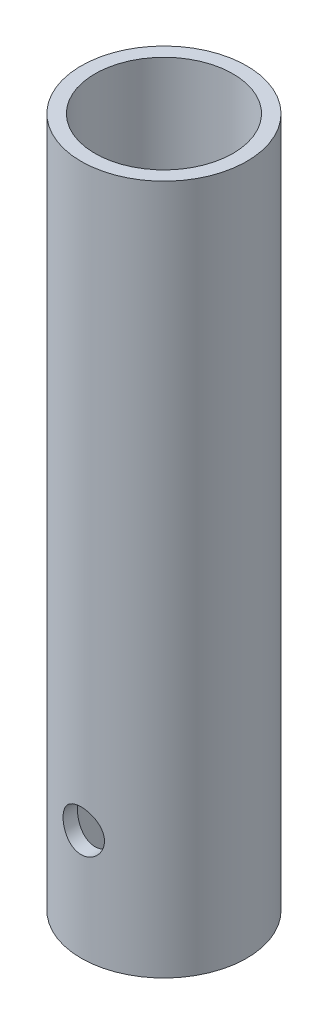
SolidWorks part; units mm, degrees
ref_plane "Ön Düzlem" through (0, 0, 0) normal (0, 0, 1) x (1, 0, 0)
ref_plane "Üst Düzlem" through (0, 0, 0) normal (0, 1, 0) x (1, 0, 0)
ref_plane "Sağ Düzlem" through (0, 0, 0) normal (1, 0, 0) x (0, 0, -1)
sketch "Sketch1" plane through (0, 0, 0) normal (0, 1, 0) x (1, 0, 0)
  circle A0 centre (0, 0) radius 6
  dimension "D1" = 12
extrude "Extrude-Thin1" add sketch "Sketch1" along normal blind 50 thin thin type one direction reverse wall 1
sketch "Sketch2" plane through (0, 0, 0) normal (0, 0, 1) x (1, 0, 0)
  circle A0 centre (0, 8) radius 1.5
  dimension "D1" = 3
  dimension "D2" = 8
extrude "Cut-Extrude1" cut sketch "Sketch2" against normal through all both and the other way through all
